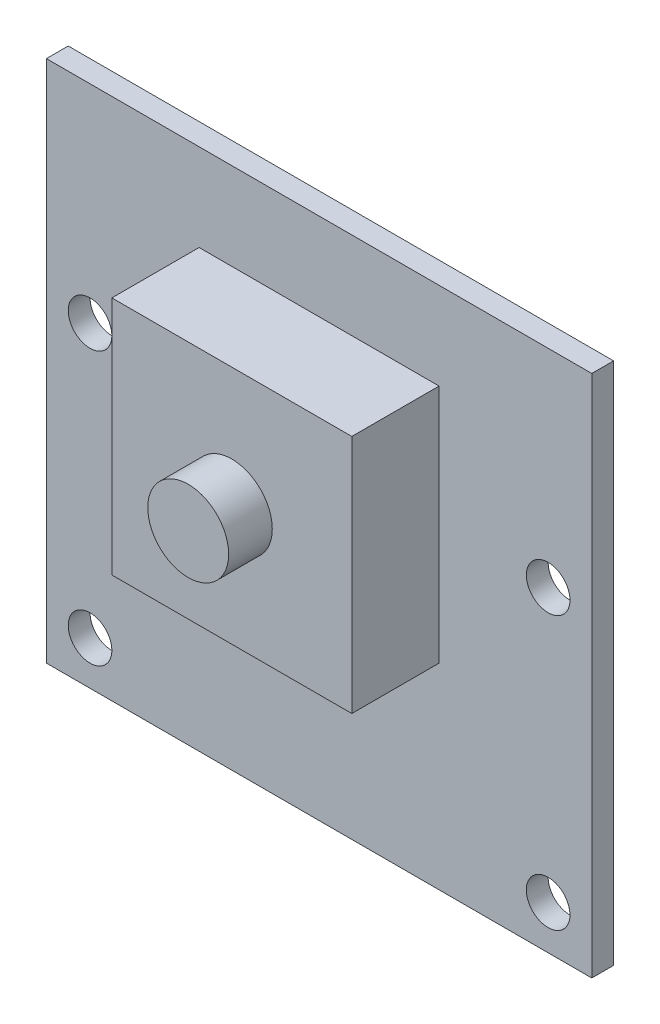
SolidWorks part; units mm, degrees
ref_plane "Front Plane" through (0, 0, 0) normal (0, 0, 1) x (1, 0, 0)
ref_plane "Top Plane" through (0, 0, 0) normal (0, 1, 0) x (1, 0, 0)
ref_plane "Right Plane" through (0, 0, 0) normal (1, 0, 0) x (0, 0, -1)
sketch "Sketch1" plane through (0, 0, 0) normal (0, 0, 1) x (1, 0, 0)
  line L1 (0, 0) -> (25, 0)
  line L2 (0, 0) -> (0, 24)
  line L3 (0, 24) -> (25, 24)
  line L4 (25, 0) -> (25, 24)
  circle A0 centre (2, 2) radius 1
  circle A1 centre (23, 2) radius 1
  circle A2 centre (2, 14.5) radius 1
  circle A3 centre (23, 14.5) radius 1
  dimension "D3" = 2
  dimension "D7" = 14.5
  dimension "D1" = 24
  dimension "D2" = 25
  dimension "D4" = 2
  dimension "D5" = 2
  dimension "D6" = 2
extrude "Boss-Extrude1" add sketch "Sketch1" along normal blind 1
sketch "Sketch2" plane through (0, 0, 1) normal (0, 0, 1) x (1, 0, 0)
  line L0 (25, 24) -> (0, 24) construction
  line L1 (7, 20) -> (18, 20)
  line L2 (7, 20) -> (7, 9)
  line L3 (7, 9) -> (18, 9)
  line L4 (18, 20) -> (18, 9)
  circle A0 centre (2, 14.5) radius 1 construction
  point P6 (12.5, 24)
  point P7 (12.5, 20)
  point P8 (7, 14.5)
  dimension "D3" = 0
  dimension "D1" = 11
  dimension "D2" = 11
extrude "Boss-Extrude2" add sketch "Sketch2" along normal blind 4
sketch "Sketch3" plane through (0, 0, 5) normal (0, 0, 1) x (1, 0, 0)
  line L0 (7, 20) -> (7, 9) construction
  line L1 (18, 20) -> (7, 20) construction
  circle A0 centre (12.5, 14.5) radius 1.8538
  point P4 (7, 14.5)
  point P7 (12.5, 20)
  dimension "D1" = 0
  dimension "D2" = 0
extrude "Boss-Extrude3" add sketch "Sketch3" along normal blind 2
